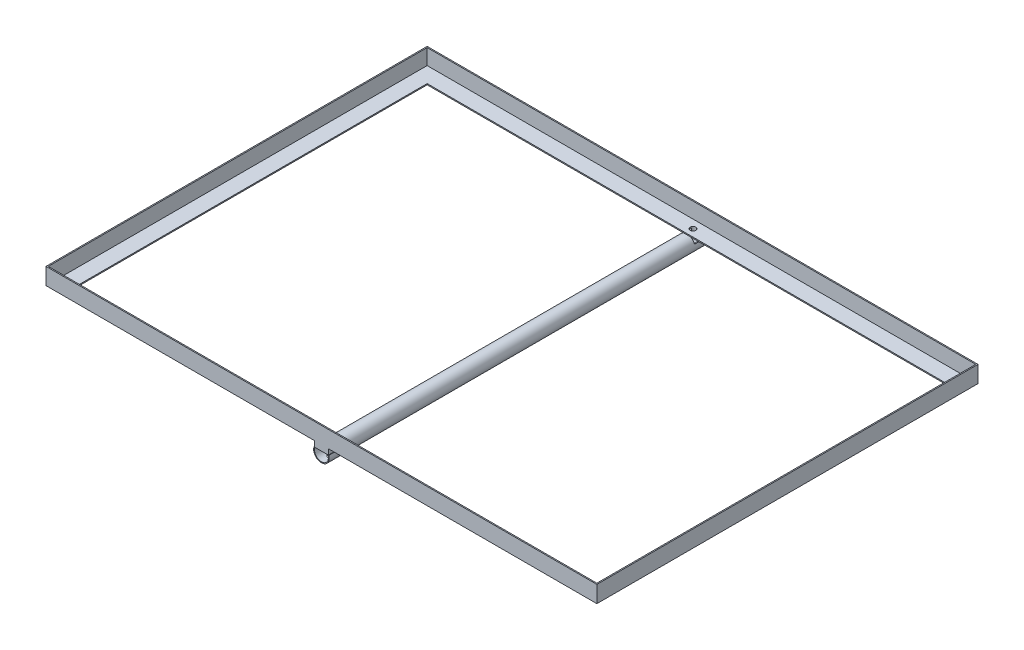
SolidWorks part; units mm, degrees
ref_plane "Front Plane" through (0, 0, 0) normal (0, 0, 1) x (1, 0, 0)
ref_plane "Top Plane" through (0, 0, 0) normal (0, 1, 0) x (1, 0, 0)
ref_plane "Right Plane" through (0, 0, 0) normal (1, 0, 0) x (0, 0, -1)
sketch "Sketch2" plane through (0, 0, 0) normal (0, 0, 1) x (1, 0, 0)
  circle A0 centre (-96.234, 31.7788) radius 14
  circle A1 centre (-96.234, 31.7788) radius 12.5
  dimension "D1" = 28
  dimension "D2" = 25
extrude "Boss-Extrude3" add sketch "Sketch2" along normal blind 800
sketch "Sketch3" plane through (0, 0, 800) normal (0, 0, 1) x (1, 0, 0)
  line L1 (-122.4791, 50.2641) -> (-71.7765, 50.2641)
  line L2 (-122.4791, 50.2641) -> (-122.4791, 35.9832)
  line L3 (-122.4791, 35.9832) -> (-71.7765, 35.9832)
  line L4 (-71.7765, 50.2641) -> (-71.7765, 35.9832)
extrude "Cut-Extrude2" cut sketch "Sketch3" against normal blind 800
sketch "Sketch5" plane through (0, 35.9832, 0) normal (0, 1, 0) x (1, 0, 0)
  line L0 (-108.734, 0) -> (-108.734, -800) construction
  line L1 (-108.734, -50) -> (-83.734, -50)
  line L2 (-108.734, -50) -> (-108.734, -80)
  line L3 (-108.734, -80) -> (-83.734, -80)
  line L4 (-83.734, -50) -> (-83.734, -80)
  line L5 (-83.734, -800) -> (-83.734, 0) construction
  line L6 (-105.234, -800) -> (-87.234, -800) construction
  line L7 (-108.734, -720) -> (-83.734, -720)
  line L8 (-108.734, -720) -> (-108.734, -750)
  line L9 (-108.734, -750) -> (-83.734, -750)
  line L10 (-83.734, -720) -> (-83.734, -750)
  line L11 (-87.234, 0) -> (-105.234, 0) construction
  point P12 (-108.734, -65)
  point P15 (-96.234, -800)
  dimension "D1" = 15
  dimension "D2" = 30
  dimension "D3" = 50
  dimension "D4" = 50
extrude "Boss-Extrude4" add sketch "Sketch5" along normal blind 10
sketch "Sketch7" plane through (0, 45.9832, 0) normal (0, 1, 0) x (1, 0, 0)
  line L1 (-591.234, -65) -> (398.766, -65)
  line L2 (-591.234, -65) -> (-591.234, -750)
  line L3 (-591.234, -750) -> (398.766, -750)
  line L4 (398.766, -65) -> (398.766, -750)
  line L5 (-561.234, -95) -> (-561.234, -720)
  line L6 (-561.234, -720) -> (368.766, -720)
  line L7 (368.766, -95) -> (368.766, -720)
  line L8 (-561.234, -95) -> (368.766, -95)
  line L9 (-96.234, -800) -> (-96.234, 0) construction
  dimension "D1" = 990
  dimension "D2" = 685
  dimension "D3" = 495
  dimension "D5" = 495
  dimension "D4" = 30
extrude "Boss-Extrude7" add sketch "Sketch7" along normal blind 30
sketch "Sketch8" plane through (0, 75.9832, 0) normal (0, 1, 0) x (1, 0, 0)
  line L0 (398.766, -65) -> (-591.234, -65) construction
  line L1 (-589.234, -67) -> (396.766, -67)
  line L2 (-589.234, -67) -> (-589.234, -748)
  line L3 (-589.234, -748) -> (396.766, -748)
  line L4 (396.766, -67) -> (396.766, -748)
  line L5 (-591.234, -65) -> (-591.234, -750) construction
  line L6 (398.766, -750) -> (398.766, -65) construction
  line L7 (-591.234, -750) -> (398.766, -750) construction
  dimension "D1" = 2
  dimension "D2" = 2
  dimension "D3" = 2
  dimension "D4" = 2
extrude "Cut-Extrude3" cut sketch "Sketch8" against normal blind 28
sketch "Sketch9" plane through (0, 47.9832, 0) normal (0, 1, 0) x (1, 0, 0)
  line L0 (-589.234, -748) -> (396.766, -748) construction
  line L1 (396.766, -67) -> (-589.234, -67) construction
  circle A0 centre (-96.4324, -82) radius 5
  circle A1 centre (-96.4324, -733) radius 5
  dimension "D1" = 10
  dimension "D3" = 10
  dimension "D4" = 15
  dimension "D2" = 15
extrude "Cut-Extrude4" cut sketch "Sketch9" against normal blind 40
sketch "Sketch13" plane through (0, 0, 80) normal (0, 0, 1) x (1, 0, 0)
  circle A0 centre (-96.234, 31.7788) radius 15
  circle A1 centre (-96.234, 31.7788) radius 35
  dimension "D1" = 20
sketch "Sketch15" plane through (0, 47.9832, 0) normal (0, 1, 0) x (1, 0, 0)
  line L0 (-661.234, 30) -> (-661.234, -830)
  line L1 (-581.234, -50) -> (398.766, -50)
  line L2 (-581.234, -50) -> (-581.234, -750)
  line L3 (-581.234, -750) -> (398.766, -750)
  line L4 (398.766, -50) -> (398.766, -750)
  line L5 (-661.234, -830) -> (478.766, -830)
  line L6 (478.766, 30) -> (478.766, -830)
  line L7 (-661.234, 30) -> (478.766, 30)
  dimension "D1" = 80
extrude "Cut-Extrude6" cut sketch "Sketch15" against normal blind 149
sketch "Sketch17" plane through (0, 0, 750) normal (0, 0, 1) x (1, 0, 0)
  line L1 (-591.234, 47.9832) -> (-581.234, 47.9832)
  line L2 (-591.234, 47.9832) -> (-591.234, 45.9832)
  line L3 (-591.234, 45.9832) -> (-581.234, 45.9832)
  line L4 (-581.234, 47.9832) -> (-581.234, 45.9832)
extrude "Boss-Extrude11" add sketch "Sketch17" against normal blind 685
sketch "Sketch20" plane through (0, 45.9832, 0) normal (0, 1, 0) x (1, 0, 0)
  line L1 (-108.734, -50) -> (-83.734, -50)
  line L2 (-108.734, -50) -> (-108.734, -65)
  line L3 (-108.734, -65) -> (-83.734, -65)
  line L4 (-83.734, -50) -> (-83.734, -65)
extrude "Cut-Extrude7" cut sketch "Sketch20" against normal blind 38
sketch "Sketch22" plane through (0, 0, 720) normal (0, 0, -1) x (-1, 0, 0)
  circle A0 centre (96.234, 31.7788) radius 12.5
  circle A1 centre (96.234, 31.7788) radius 14
extrude "Boss-Extrude13" add sketch "Sketch22" along normal blind 627
sketch "Sketch23" plane through (0, 47.9832, 0) normal (0, 1, 0) x (1, 0, 0)
  line L0 (398.766, -65) -> (-591.234, -65) construction
  line L1 (-132.1602, -19.8237) -> (-73.1136, -19.8237)
  line L2 (-132.1602, -19.8237) -> (-132.1602, -65)
  line L3 (-132.1602, -65) -> (-73.1136, -65)
  line L4 (-73.1136, -19.8237) -> (-73.1136, -65)
extrude "Cut-Extrude8" cut sketch "Sketch23" against normal blind 627
